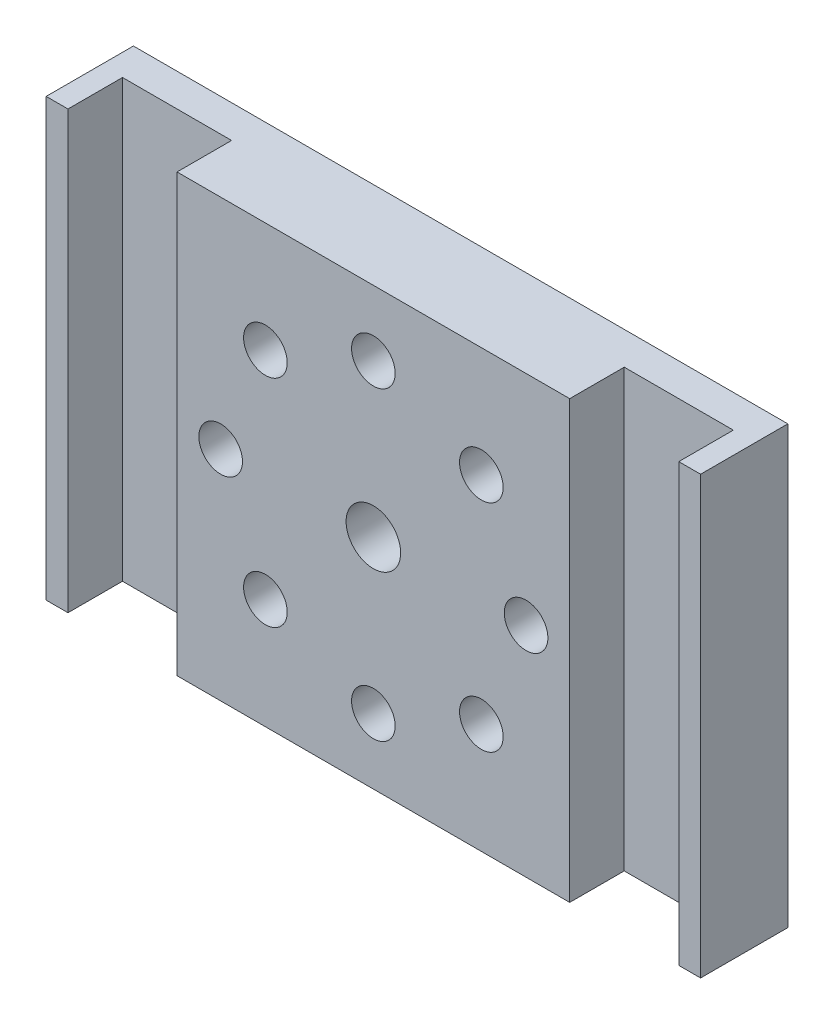
SolidWorks part; units mm, degrees
ref_plane "Plan de face" through (0, 0, 0) normal (0, 0, 1) x (1, 0, 0)
ref_plane "Plan de dessus" through (0, 0, 0) normal (0, 1, 0) x (1, 0, 0)
ref_plane "Plan de droite" through (0, 0, 0) normal (1, 0, 0) x (0, 0, -1)
sketch "Esquisse1" plane through (0, 0, 0) normal (0, 0, 1) x (1, 0, 0)
  line L0 (-30, -20) -> (-30, 20)
  line L1 (-30, 20) -> (30, 20)
  line L2 (30, 20) -> (30, -20)
  line L3 (30, -20) -> (-30, -20)
  circle A0 centre (0, 0) radius 2.5
  circle A1 centre (9.8995, 9.8995) radius 2
  circle A2 centre (0, 14) radius 2
  circle A3 centre (14, 0) radius 2
  circle A4 centre (9.8995, -9.8995) radius 2
  circle A5 centre (0, -14) radius 2
  circle A6 centre (-9.8995, -9.8995) radius 2
  circle A7 centre (-14, 0) radius 2
  circle A8 centre (-9.8995, 9.8995) radius 2
extrude "Extrusion1" add sketch "Esquisse1" along normal blind 8
sketch "Esquisse2" plane through (0, 0, 0) normal (0, 0, 1) x (1, 0, 0)
  circle A0 centre (0, 0) radius 4
extrude "Extrusion2" cut sketch "Esquisse2" along normal blind 4
sketch "Esquisse3" plane through (0, -20, 0) normal (0, -1, 0) x (1, 0, 0)
  line L0 (-30, 8) -> (-30, 0) construction
  line L2 (-30, 4) -> (30, 4) construction
  line L4 (30, 8) -> (30, 0) construction
  circle A1 centre (-15.5, 4) radius 2
  circle A2 centre (15.5, 4) radius 2
extrude "Extrusion3" cut sketch "Esquisse3" against normal blind 15
sketch "Esquisse4" plane through (0, 20, 0) normal (0, 1, 0) x (1, 0, 0)
  line L0 (-28, -8) -> (-18, -8)
  line L2 (-28, -8) -> (-28, -3)
  line L3 (-28, -3) -> (-18, -3)
  line L4 (-18, -3) -> (-18, -8)
  line L5 (18, -8) -> (28, -8)
  line L8 (18, -3) -> (18, -8)
  line L9 (28, -3) -> (18, -3)
  line L10 (28, -8) -> (28, -3)
extrude "Extrusion4" cut sketch "Esquisse4" against normal through all
